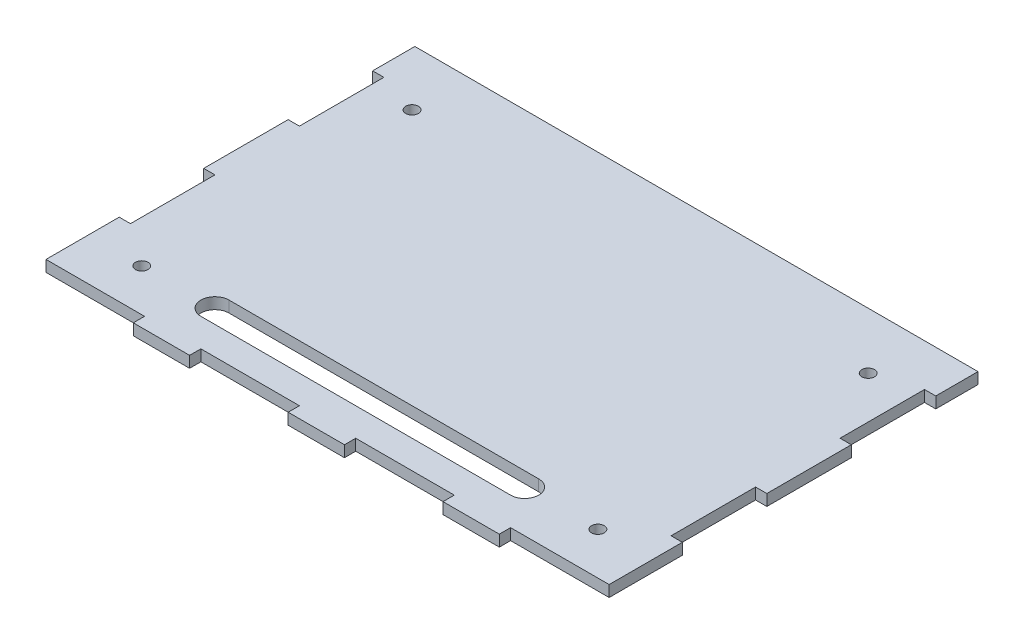
SolidWorks part; units mm, degrees
ref_plane "Plano frontal" through (0, 0, 0) normal (0, 0, 1) x (1, 0, 0)
ref_plane "Plano superior" through (0, 0, 0) normal (0, 1, 0) x (1, 0, 0)
ref_plane "Plano direito" through (0, 0, 0) normal (1, 0, 0) x (0, 0, -1)
sketch "Esboço1" plane through (0, 0, 0) normal (0, 1, 0) x (1, 0, 0)
  line L0 (-100, 75) -> (100, -75) construction
  line L1 (-100, 75) -> (100, 75)
  line L2 (-100, 75) -> (-100, -75)
  line L3 (-100, -75) -> (100, -75)
  line L4 (100, 75) -> (100, -75)
  point P4 (0, 0)
  dimension "D1" = 200
  dimension "D2" = 150
extrude "Ressalto-extrusão1" add sketch "Esboço1" along normal blind 4
sketch "Esboço2" plane through (0, 4, 0) normal (0, 1, 0) x (1, 0, 0)
  line L0 (-65, -75) -> (-65, -71)
  line L1 (-100, -75) -> (100, -75) construction
  line L2 (-65, -71) -> (-45, -71)
  line L3 (-45, -71) -> (-45, -75)
  line L4 (-45, -75) -> (-10, -75)
  line L5 (-10, -75) -> (-10, -71)
  line L6 (-10, -71) -> (10, -71)
  line L7 (10, -71) -> (10, -75)
  line L8 (10, -75) -> (45, -75)
  line L9 (45, -75) -> (45, -71)
  line L10 (45, -71) -> (65, -71)
  line L11 (65, -71) -> (65, -75)
  line L12 (-100, 75) -> (-100, -75) construction
  line L13 (0, 0) -> (0, 75) construction
  line L15 (10, -71) -> (45, -71)
  line L17 (-65, -75) -> (-100, -75)
  line L18 (-100, -75) -> (-100, -71)
  line L19 (-100, -71) -> (-65, -71)
  line L20 (-45, -71) -> (-10, -71)
  line L21 (65, -71) -> (100, -71)
  line L22 (100, -75) -> (100, 75) construction
  line L23 (100, -45) -> (96, -45)
  line L24 (96, -45) -> (96, -15)
  line L25 (96, -15) -> (100, -15)
  line L26 (100, -15) -> (100, 15)
  line L27 (100, 15) -> (96, 15)
  line L28 (96, 15) -> (96, 45)
  line L29 (96, 45) -> (100, 45)
  line L30 (100, 75) -> (-100, 75) construction
  line L31 (-100, -15) -> (-100, -45)
  line L32 (-100, 45) -> (-100, 15)
  line L33 (-96, 45) -> (-100, 45)
  line L34 (100, 45) -> (100, 15)
  line L35 (100, -15) -> (100, -45)
  line L36 (-96, 15) -> (-96, 45)
  line L37 (-100, 15) -> (-96, 15)
  line L38 (-100, -15) -> (-100, 15)
  line L39 (-96, -15) -> (-100, -15)
  line L40 (-96, -45) -> (-96, -15)
  line L41 (-100, -45) -> (-96, -45)
  line M8 (-100, 75) -> (-100, -75)
  line M9 (-100, -75) -> (100, -75)
  line M10 (100, -75) -> (100, 75)
  dimension "D1" = 35
  dimension "D2" = 35
  dimension "D3" = 35
  dimension "D4" = 20
  dimension "D5" = 20
  dimension "D6" = 20
  dimension "D7" = 4
  dimension "D8" = 30
  dimension "D9" = 30
  dimension "D10" = 30
  dimension "D11" = 30
  dimension "D12" = 4
extrude "Corte-extrusão1" cut sketch "Esboço2" against normal through all contours L20 L3 L5 M9 | L15 L7 L9 M9 | L21 L11 M9 M10 | L19 L0 M8 M9 | L27 L28 L29 L34 | L35 L23 L24 L25 | L37 L36 L33 L32 | L31 L41 L40 L39
sketch "Esboço3" plane through (0, 4, 0) normal (0, 1, 0) x (1, 0, 0)
  line L0 (100, 45) -> (100, 75) construction
  line L1 (-100, 75) -> (100, 75)
  line L2 (-100, 75) -> (-100, 60)
  line L3 (-100, 60) -> (100, 60)
  line L4 (100, 75) -> (100, 60)
  dimension "D1" = 15
extrude "Corte-extrusão2" cut sketch "Esboço3" against normal through all
hole_wizard "Broca de rosquear para tarraxa de M41" positions "3DSketch1" profile "Esboço4" hole size "M4" standard "ISO" end condition through all
sketch3d "3DSketch1"
  line L1 (-100, 4, -60) -> (100, 4, -60) construction
  line L3 (-100, 4, 71) -> (-65, 4, 71) construction
  line L5 (65, 4, 71) -> (100, 4, 71) construction
  line L7 (-96, 4, -15) -> (-96, 4, -45) construction
  line L8 (96, 4, -15) -> (96, 4, -45) construction
  line L9 (-96, 4, 45) -> (-96, 4, 15) construction
  line L10 (96, 4, 45) -> (96, 4, 15) construction
  point P0 (-81, 4, -40)
  point P2 (-81, 4, 56)
  point P4 (81, 4, 56)
  point P6 (81, 4, -40)
  dimension "D1" = 15
  dimension "D2" = 20
  dimension "D3" = 15
  dimension "D4" = 15
  dimension "D5" = 15
  dimension "D6" = 15
  dimension "D7" = 15
  dimension "D8" = 20
sketch "Esboço4" plane through (-81, 4, -40) normal (1, 0, 0) x (0, 0, 1)
  line L0 (0, 0) -> (0, 4)
  line L1 (0, 4) -> (2.25, 4)
  line L2 (2.25, 4) -> (2.25, 0)
  line L5 (2.25, 0) -> (0, 0)
  line L11 (0, -6.35) -> (0, 107.95) construction
  dimension "Thru Hole Dia." = 4.5
  dimension "Thru Hole Depth" = 4
sketch "Esboço5" plane through (0, 4, 0) normal (0, 1, 0) x (1, 0, 0)
  line L0 (55, -56) -> (-55, -56) construction
  line L1 (55, -61) -> (-55, -61)
  line L2 (55, -51) -> (-55, -51)
  line L3 (-85, -56) -> (83.35, -56) construction
  line L4 (0, 60) -> (0, -75) construction
  arc A0 (55, -61) -> (55, -51) centre (55, -56) ccw
  arc A1 (-55, -51) -> (-55, -61) centre (-55, -56) ccw
  circle A5 centre (-81, -56) radius 2.25
  circle A6 centre (-81, -56) radius 2.25 construction
  point P2 (0, -56)
  dimension "D2" = 5
  dimension "D1" = 110
extrude "Corte-extrusão3" cut sketch "Esboço5" against normal through all
